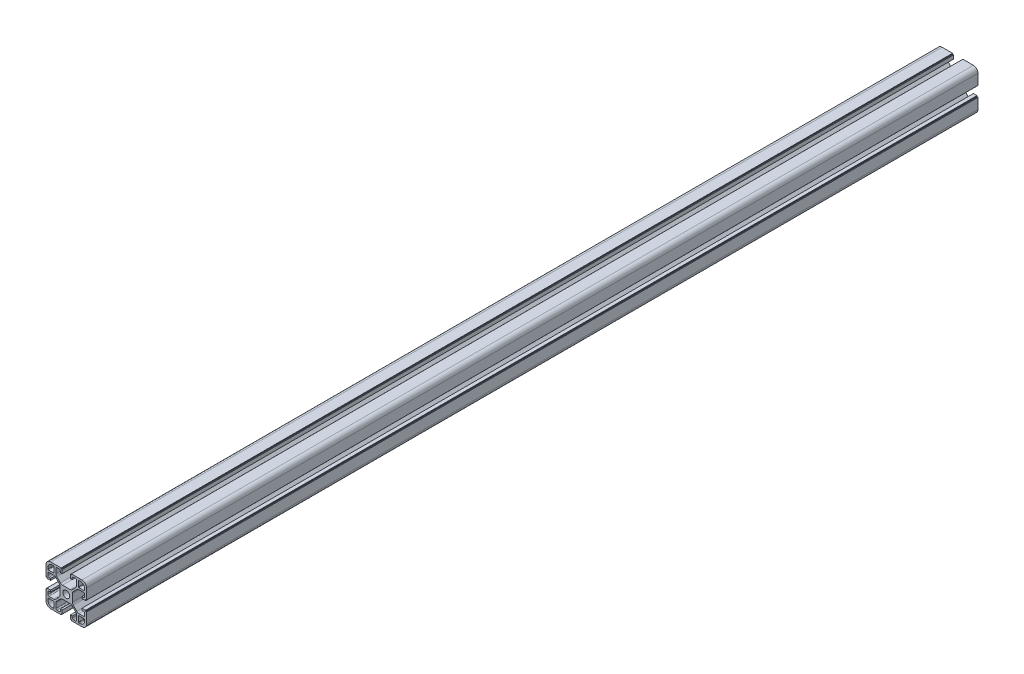
SolidWorks part; units mm, degrees
ref_plane "Front Plane" through (0, 0, 0) normal (0, 0, 1) x (1, 0, 0)
ref_plane "Top Plane" through (0, 0, 0) normal (0, 1, 0) x (1, 0, 0)
ref_plane "Right Plane" through (0, 0, 0) normal (1, 0, 0) x (0, 0, -1)
sketch "Sketch2" plane through (0, 0, 0) normal (0, 0, 1) x (1, 0, 0)
  line L0 (84.1702, 31.7204) -> (84.1702, 42.1204)
  line L1 (44.1702, 62.7204) -> (44.1702, 52.3204)
  line L2 (48.6702, 27.2204) -> (59.0702, 27.2204)
  line L3 (79.6702, 67.2204) -> (69.2702, 67.2204)
  line L4 (84.1702, 52.3204) -> (84.1702, 62.7204)
  line L5 (58.8702, 67.2204) -> (48.6702, 67.2204)
  line L6 (44.1702, 42.1204) -> (44.1702, 31.7204)
  line L7 (69.2702, 27.2204) -> (79.6702, 27.2204)
  line L8 (48.6702, 27.2204) -> (59.0702, 27.2204)
  line L9 (44.1702, 42.1204) -> (44.1702, 31.7204)
  line L10 (44.1702, 42.1204) -> (44.7702, 42.1204)
  line L11 (44.9702, 42.3204) -> (44.9702, 42.9204)
  line L12 (48.6702, 43.1204) -> (45.1702, 43.1204)
  line L13 (48.6702, 41.3204) -> (48.6702, 43.1204)
  line L14 (46.9702, 41.3204) -> (48.6702, 41.3204)
  line L15 (45.9702, 37.9704) -> (45.9702, 40.3204)
  line L16 (51.6169, 36.9704) -> (46.9702, 36.9704)
  line L17 (57.2915, 41.4024) -> (53.7382, 37.8491)
  line L18 (58.1702, 50.9171) -> (58.1702, 43.5237)
  line L19 (53.7382, 56.5917) -> (57.2915, 53.0384)
  line L20 (46.9702, 57.4704) -> (51.6169, 57.4704)
  line L21 (45.9702, 54.1204) -> (45.9702, 56.4704)
  line L22 (48.6702, 53.1204) -> (46.9702, 53.1204)
  line L23 (48.6702, 51.3204) -> (48.6702, 53.1204)
  line L24 (45.1702, 51.3204) -> (48.6702, 51.3204)
  line L25 (44.9702, 51.5204) -> (44.9702, 52.1204)
  line L26 (44.7702, 52.3204) -> (44.1702, 52.3204)
  line L27 (44.1702, 62.7204) -> (44.1702, 52.3204)
  line L28 (59.0702, 67.2204) -> (48.6702, 67.2204)
  line L29 (59.0702, 67.2204) -> (59.0702, 66.6204)
  line L30 (59.2702, 66.4204) -> (60.0702, 66.4204)
  line L31 (60.0702, 62.7204) -> (60.0702, 66.4204)
  line L32 (58.2702, 62.7204) -> (60.0702, 62.7204)
  line L33 (58.2702, 64.4204) -> (58.2702, 62.7204)
  line L34 (54.9202, 65.4204) -> (57.2702, 65.4204)
  line L35 (53.9202, 59.7737) -> (53.9202, 64.4204)
  line L36 (58.3522, 54.0991) -> (54.7989, 57.6524)
  line L37 (67.8669, 53.2204) -> (60.4735, 53.2204)
  line L38 (73.5415, 57.6524) -> (69.9882, 54.0991)
  line L39 (74.4202, 64.4204) -> (74.4202, 59.7737)
  line L40 (71.0702, 65.4204) -> (73.4202, 65.4204)
  line L41 (70.0702, 62.7204) -> (70.0702, 64.4204)
  line L42 (68.2702, 62.7204) -> (70.0702, 62.7204)
  line L43 (68.2702, 66.2204) -> (68.2702, 62.7204)
  line L44 (68.4702, 66.4204) -> (69.2702, 66.4204)
  line L45 (69.2702, 66.4204) -> (69.2702, 67.2204)
  line L46 (79.6702, 67.2204) -> (69.4702, 67.2204)
  line L47 (84.1702, 52.3204) -> (84.1702, 62.7204)
  line L48 (84.1702, 52.3204) -> (83.5702, 52.3204)
  line L49 (83.3702, 52.1204) -> (83.3702, 51.5204)
  line L50 (79.6702, 51.3204) -> (83.1702, 51.3204)
  line L51 (79.6702, 53.1204) -> (79.6702, 51.3204)
  line L52 (81.3702, 53.1204) -> (79.6702, 53.1204)
  line L53 (82.3702, 56.4704) -> (82.3702, 54.1204)
  line L54 (76.7235, 57.4704) -> (81.3702, 57.4704)
  line L55 (71.0489, 53.0384) -> (74.6022, 56.5917)
  line L56 (70.1702, 43.5237) -> (70.1702, 50.9171)
  line L57 (74.6022, 37.8491) -> (71.0489, 41.4024)
  line L58 (81.3702, 36.9704) -> (76.7235, 36.9704)
  line L59 (82.3702, 40.3204) -> (82.3702, 37.9704)
  line L60 (79.6702, 41.3204) -> (81.3702, 41.3204)
  line L61 (79.6702, 43.1204) -> (79.6702, 41.3204)
  line L62 (83.1702, 43.1204) -> (79.6702, 43.1204)
  line L63 (83.3702, 42.9204) -> (83.3702, 42.3204)
  line L64 (83.5702, 42.1204) -> (84.1702, 42.1204)
  line L65 (84.1702, 31.7204) -> (84.1702, 42.1204)
  line L66 (69.2702, 27.2204) -> (79.6702, 27.2204)
  line L67 (69.2702, 27.2204) -> (69.2702, 27.8204)
  line L68 (69.0702, 28.0204) -> (68.4702, 28.0204)
  line L69 (68.2702, 31.7204) -> (68.2702, 28.2204)
  line L70 (70.0702, 31.7204) -> (68.2702, 31.7204)
  line L71 (70.0702, 30.0204) -> (70.0702, 31.7204)
  line L72 (73.4202, 29.0204) -> (71.0702, 29.0204)
  line L73 (74.4202, 34.6671) -> (74.4202, 30.0204)
  line L74 (69.9882, 40.3417) -> (73.5415, 36.7884)
  line L75 (60.4735, 41.2204) -> (67.8669, 41.2204)
  line L76 (54.7989, 36.7884) -> (58.3522, 40.3417)
  line L77 (53.9202, 30.0204) -> (53.9202, 34.6671)
  line L78 (57.2702, 29.0204) -> (54.9202, 29.0204)
  line L79 (58.2702, 31.7204) -> (58.2702, 30.0204)
  line L80 (60.0702, 31.7204) -> (58.2702, 31.7204)
  line L81 (60.0702, 28.2204) -> (60.0702, 31.7204)
  line L82 (59.8702, 28.0204) -> (59.2702, 28.0204)
  line L83 (59.0702, 27.8204) -> (59.0702, 27.2204)
  line L84 (82.3702, 34.6704) -> (82.3702, 33.5204)
  line L85 (76.7202, 35.1704) -> (81.8702, 35.1704)
  line L86 (76.2202, 29.5204) -> (76.2202, 34.6704)
  line L87 (77.8702, 29.0204) -> (76.7202, 29.0204)
  line L88 (51.6202, 29.0204) -> (50.4702, 29.0204)
  line L89 (52.1202, 34.6704) -> (52.1202, 29.5204)
  line L90 (46.4702, 35.1704) -> (51.6202, 35.1704)
  line L91 (45.9702, 33.5204) -> (45.9702, 34.6704)
  line L92 (45.9702, 59.7704) -> (45.9702, 60.9204)
  line L93 (51.6202, 59.2704) -> (46.4702, 59.2704)
  line L94 (52.1202, 64.9204) -> (52.1202, 59.7704)
  line L95 (50.4702, 65.4204) -> (51.6202, 65.4204)
  line L96 (76.7202, 65.4204) -> (77.8702, 65.4204)
  line L97 (76.2202, 59.7704) -> (76.2202, 64.9204)
  line L98 (81.8702, 59.2704) -> (76.7202, 59.2704)
  line L99 (82.3702, 60.9204) -> (82.3702, 59.7704)
  line L100 (71.0702, 65.4204) -> (73.4202, 65.4204)
  line L101 (70.0702, 62.7204) -> (70.0702, 64.4204)
  line L102 (68.2702, 62.7204) -> (70.0702, 62.7204)
  line L103 (68.2702, 66.2204) -> (68.2702, 62.7204)
  line L104 (60.0702, 62.7204) -> (60.0702, 66.2204)
  line L105 (58.2702, 62.7204) -> (60.0702, 62.7204)
  line L106 (58.2702, 64.4204) -> (58.2702, 62.7204)
  line L107 (54.9202, 65.4204) -> (57.2702, 65.4204)
  line L108 (53.9202, 59.7737) -> (53.9202, 64.4204)
  line L109 (58.3522, 54.0991) -> (54.7989, 57.6524)
  line L110 (67.8669, 53.2204) -> (60.4735, 53.2204)
  line L111 (73.5415, 57.6524) -> (69.9882, 54.0991)
  line L112 (74.4202, 64.4204) -> (74.4202, 59.7737)
  line L113 (59.2702, 66.4204) -> (59.8702, 66.4204)
  line L114 (59.0702, 67.0204) -> (59.0702, 66.6204)
  line L115 (69.2702, 66.6204) -> (69.2702, 67.0204)
  line L116 (68.4702, 66.4204) -> (69.0702, 66.4204)
  line L117 (82.3702, 40.3204) -> (82.3702, 37.9704)
  line L118 (79.6702, 41.3204) -> (81.3702, 41.3204)
  line L119 (79.6702, 43.1204) -> (79.6702, 41.3204)
  line L120 (83.1702, 43.1204) -> (79.6702, 43.1204)
  line L121 (79.6702, 51.3204) -> (83.1702, 51.3204)
  line L122 (79.6702, 53.1204) -> (79.6702, 51.3204)
  line L123 (81.3702, 53.1204) -> (79.6702, 53.1204)
  line L124 (82.3702, 56.4704) -> (82.3702, 54.1204)
  line L125 (76.7235, 57.4704) -> (81.3702, 57.4704)
  line L126 (71.0489, 53.0384) -> (74.6022, 56.5917)
  line L127 (70.1702, 43.5237) -> (70.1702, 50.9171)
  line L128 (74.6022, 37.8491) -> (71.0489, 41.4024)
  line L129 (81.3702, 36.9704) -> (76.7235, 36.9704)
  line L130 (45.9702, 54.1204) -> (45.9702, 56.4704)
  line L131 (48.6702, 53.1204) -> (46.9702, 53.1204)
  line L132 (48.6702, 51.3204) -> (48.6702, 53.1204)
  line L133 (45.1702, 51.3204) -> (48.6702, 51.3204)
  line L134 (48.6702, 43.1204) -> (45.1702, 43.1204)
  line L135 (48.6702, 41.3204) -> (48.6702, 43.1204)
  line L136 (46.9702, 41.3204) -> (48.6702, 41.3204)
  line L137 (45.9702, 37.9704) -> (45.9702, 40.3204)
  line L138 (51.6169, 36.9704) -> (46.9702, 36.9704)
  line L139 (57.2915, 41.4024) -> (53.7382, 37.8491)
  line L140 (58.1702, 50.9171) -> (58.1702, 43.5237)
  line L141 (53.7382, 56.5917) -> (57.2915, 53.0384)
  line L142 (46.9702, 57.4704) -> (51.6169, 57.4704)
  line L143 (57.2702, 29.0204) -> (54.9202, 29.0204)
  line L144 (58.2702, 31.7204) -> (58.2702, 30.0204)
  line L145 (60.0702, 31.7204) -> (58.2702, 31.7204)
  line L146 (60.0702, 28.2204) -> (60.0702, 31.7204)
  line L147 (68.2702, 31.7204) -> (68.2702, 28.2204)
  line L148 (70.0702, 31.7204) -> (68.2702, 31.7204)
  line L149 (70.0702, 30.0204) -> (70.0702, 31.7204)
  line L150 (73.4202, 29.0204) -> (71.0702, 29.0204)
  line L151 (74.4202, 34.6671) -> (74.4202, 30.0204)
  line L152 (69.9882, 40.3417) -> (73.5415, 36.7884)
  line L153 (60.4735, 41.2204) -> (67.8669, 41.2204)
  line L154 (54.7989, 36.7884) -> (58.3522, 40.3417)
  line L155 (53.9202, 30.0204) -> (53.9202, 34.6671)
  line L156 (69.0702, 28.0204) -> (68.4702, 28.0204)
  line L157 (69.2702, 27.2204) -> (69.2702, 27.8204)
  line L158 (59.0702, 27.8204) -> (59.0702, 27.2204)
  line L159 (59.8702, 28.0204) -> (59.2702, 28.0204)
  line L160 (44.9702, 42.3204) -> (44.9702, 42.9204)
  line L161 (44.1702, 42.1204) -> (44.7702, 42.1204)
  line L162 (44.7702, 52.3204) -> (44.1702, 52.3204)
  line L163 (44.9702, 51.5204) -> (44.9702, 52.1204)
  line L164 (83.3702, 52.1204) -> (83.3702, 51.5204)
  line L165 (84.1702, 52.3204) -> (83.5702, 52.3204)
  line L166 (83.5702, 42.1204) -> (84.1702, 42.1204)
  line L167 (83.3702, 42.9204) -> (83.3702, 42.3204)
  line L168 (76.2202, 59.7704) -> (76.2202, 64.9204)
  line L169 (81.8702, 59.2704) -> (76.7202, 59.2704)
  line L170 (82.3702, 60.9204) -> (82.3702, 59.7704)
  line L171 (76.7202, 65.4204) -> (77.8702, 65.4204)
  line L172 (51.6202, 59.2704) -> (46.4702, 59.2704)
  line L173 (52.1202, 64.9204) -> (52.1202, 59.7704)
  line L174 (50.4702, 65.4204) -> (51.6202, 65.4204)
  line L175 (45.9702, 59.7704) -> (45.9702, 60.9204)
  line L176 (52.1202, 34.6704) -> (52.1202, 29.5204)
  line L177 (46.4702, 35.1704) -> (51.6202, 35.1704)
  line L178 (45.9702, 33.5204) -> (45.9702, 34.6704)
  line L179 (51.6202, 29.0204) -> (50.4702, 29.0204)
  line L180 (76.7202, 35.1704) -> (81.8702, 35.1704)
  line L181 (76.2202, 29.5204) -> (76.2202, 34.6704)
  line L182 (77.8702, 29.0204) -> (76.7202, 29.0204)
  line L183 (82.3702, 34.6704) -> (82.3702, 33.5204)
  arc A0 (60.7702, 47.2204) -> (67.5702, 47.2204) centre (64.1702, 47.2204) ccw
  arc A1 (44.1702, 31.7204) -> (48.6702, 27.2204) centre (48.6702, 31.7204) ccw
  arc A2 (44.7702, 42.1204) -> (44.9702, 42.3204) centre (44.7702, 42.3204) ccw
  arc A3 (45.1702, 43.1204) -> (44.9702, 42.9204) centre (45.1702, 42.9204) ccw
  arc A4 (46.9702, 41.3204) -> (45.9702, 40.3204) centre (46.9702, 40.3204) ccw
  arc A5 (45.9702, 37.9704) -> (46.9702, 36.9704) centre (46.9702, 37.9704) ccw
  arc A6 (51.6169, 36.9704) -> (53.7382, 37.8491) centre (51.6169, 39.9704) ccw
  arc A7 (57.2915, 41.4024) -> (58.1702, 43.5237) centre (55.1702, 43.5237) ccw
  arc A8 (58.1702, 50.9171) -> (57.2915, 53.0384) centre (55.1702, 50.9171) ccw
  arc A9 (53.7382, 56.5917) -> (51.6169, 57.4704) centre (51.6169, 54.4704) ccw
  arc A10 (46.9702, 57.4704) -> (45.9702, 56.4704) centre (46.9702, 56.4704) ccw
  arc A11 (45.9702, 54.1204) -> (46.9702, 53.1204) centre (46.9702, 54.1204) ccw
  arc A12 (44.9702, 51.5204) -> (45.1702, 51.3204) centre (45.1702, 51.5204) ccw
  arc A13 (44.9702, 52.1204) -> (44.7702, 52.3204) centre (44.7702, 52.1204) ccw
  arc A14 (48.6702, 67.2204) -> (44.1702, 62.7204) centre (48.6702, 62.7204) ccw
  arc A15 (59.0702, 66.6204) -> (59.2702, 66.4204) centre (59.2702, 66.6204) ccw
  arc A16 (58.2702, 64.4204) -> (57.2702, 65.4204) centre (57.2702, 64.4204) ccw
  arc A17 (54.9202, 65.4204) -> (53.9202, 64.4204) centre (54.9202, 64.4204) ccw
  arc A18 (53.9202, 59.7737) -> (54.7989, 57.6524) centre (56.9202, 59.7737) ccw
  arc A19 (58.3522, 54.0991) -> (60.4735, 53.2204) centre (60.4735, 56.2204) ccw
  arc A20 (67.8669, 53.2204) -> (69.9882, 54.0991) centre (67.8669, 56.2204) ccw
  arc A21 (73.5415, 57.6524) -> (74.4202, 59.7737) centre (71.4202, 59.7737) ccw
  arc A22 (74.4202, 64.4204) -> (73.4202, 65.4204) centre (73.4202, 64.4204) ccw
  arc A23 (71.0702, 65.4204) -> (70.0702, 64.4204) centre (71.0702, 64.4204) ccw
  arc A24 (68.4702, 66.4204) -> (68.2702, 66.2204) centre (68.4702, 66.2204) ccw
  arc A25 (84.1702, 62.7204) -> (79.6702, 67.2204) centre (79.6702, 62.7204) ccw
  arc A26 (83.5702, 52.3204) -> (83.3702, 52.1204) centre (83.5702, 52.1204) ccw
  arc A27 (83.1702, 51.3204) -> (83.3702, 51.5204) centre (83.1702, 51.5204) ccw
  arc A28 (81.3702, 53.1204) -> (82.3702, 54.1204) centre (81.3702, 54.1204) ccw
  arc A29 (82.3702, 56.4704) -> (81.3702, 57.4704) centre (81.3702, 56.4704) ccw
  arc A30 (76.7235, 57.4704) -> (74.6022, 56.5917) centre (76.7235, 54.4704) ccw
  arc A31 (71.0489, 53.0384) -> (70.1702, 50.9171) centre (73.1702, 50.9171) ccw
  arc A32 (70.1702, 43.5237) -> (71.0489, 41.4024) centre (73.1702, 43.5237) ccw
  arc A33 (74.6022, 37.8491) -> (76.7235, 36.9704) centre (76.7235, 39.9704) ccw
  arc A34 (81.3702, 36.9704) -> (82.3702, 37.9704) centre (81.3702, 37.9704) ccw
  arc A35 (82.3702, 40.3204) -> (81.3702, 41.3204) centre (81.3702, 40.3204) ccw
  arc A36 (83.3702, 42.9204) -> (83.1702, 43.1204) centre (83.1702, 42.9204) ccw
  arc A37 (83.3702, 42.3204) -> (83.5702, 42.1204) centre (83.5702, 42.3204) ccw
  arc A38 (79.6702, 27.2204) -> (84.1702, 31.7204) centre (79.6702, 31.7204) ccw
  arc A39 (69.2702, 27.8204) -> (69.0702, 28.0204) centre (69.0702, 27.8204) ccw
  arc A40 (68.2702, 28.2204) -> (68.4702, 28.0204) centre (68.4702, 28.2204) ccw
  arc A41 (70.0702, 30.0204) -> (71.0702, 29.0204) centre (71.0702, 30.0204) ccw
  arc A42 (73.4202, 29.0204) -> (74.4202, 30.0204) centre (73.4202, 30.0204) ccw
  arc A43 (74.4202, 34.6671) -> (73.5415, 36.7884) centre (71.4202, 34.6671) ccw
  arc A44 (69.9882, 40.3417) -> (67.8669, 41.2204) centre (67.8669, 38.2204) ccw
  arc A45 (60.4735, 41.2204) -> (58.3522, 40.3417) centre (60.4735, 38.2204) ccw
  arc A46 (54.7989, 36.7884) -> (53.9202, 34.6671) centre (56.9202, 34.6671) ccw
  arc A47 (53.9202, 30.0204) -> (54.9202, 29.0204) centre (54.9202, 30.0204) ccw
  arc A48 (57.2702, 29.0204) -> (58.2702, 30.0204) centre (57.2702, 30.0204) ccw
  arc A49 (59.8702, 28.0204) -> (60.0702, 28.2204) centre (59.8702, 28.2204) ccw
  arc A50 (59.2702, 28.0204) -> (59.0702, 27.8204) centre (59.2702, 27.8204) ccw
  arc A51 (82.3702, 34.6704) -> (81.8702, 35.1704) centre (81.8702, 34.6704) ccw
  arc A52 (76.7202, 35.1704) -> (76.2202, 34.6704) centre (76.7202, 34.6704) ccw
  arc A53 (76.2202, 29.5204) -> (76.7202, 29.0204) centre (76.7202, 29.5204) ccw
  arc A54 (77.8702, 29.0204) -> (82.3702, 33.5204) centre (77.8702, 33.5204) ccw
  arc A55 (51.6202, 29.0204) -> (52.1202, 29.5204) centre (51.6202, 29.5204) ccw
  arc A56 (52.1202, 34.6704) -> (51.6202, 35.1704) centre (51.6202, 34.6704) ccw
  arc A57 (46.4702, 35.1704) -> (45.9702, 34.6704) centre (46.4702, 34.6704) ccw
  arc A58 (45.9702, 33.5204) -> (50.4702, 29.0204) centre (50.4702, 33.5204) ccw
  arc A59 (45.9702, 59.7704) -> (46.4702, 59.2704) centre (46.4702, 59.7704) ccw
  arc A60 (51.6202, 59.2704) -> (52.1202, 59.7704) centre (51.6202, 59.7704) ccw
  arc A61 (52.1202, 64.9204) -> (51.6202, 65.4204) centre (51.6202, 64.9204) ccw
  arc A62 (50.4702, 65.4204) -> (45.9702, 60.9204) centre (50.4702, 60.9204) ccw
  arc A63 (76.7202, 65.4204) -> (76.2202, 64.9204) centre (76.7202, 64.9204) ccw
  arc A64 (76.2202, 59.7704) -> (76.7202, 59.2704) centre (76.7202, 59.7704) ccw
  arc A65 (81.8702, 59.2704) -> (82.3702, 59.7704) centre (81.8702, 59.7704) ccw
  arc A66 (82.3702, 60.9204) -> (77.8702, 65.4204) centre (77.8702, 60.9204) ccw
  arc A67 (67.5702, 47.2204) -> (60.7702, 47.2204) centre (64.1702, 47.2204) ccw
  arc A68 (60.7702, 47.2204) -> (67.5702, 47.2204) centre (64.1702, 47.2204) ccw
  arc A69 (67.5702, 47.2204) -> (60.7702, 47.2204) centre (64.1702, 47.2204) ccw
  arc A70 (71.0702, 65.4204) -> (70.0702, 64.4204) centre (71.0702, 64.4204) ccw
  arc A71 (54.9202, 65.4204) -> (53.9202, 64.4204) centre (54.9202, 64.4204) ccw
  arc A72 (58.2702, 64.4204) -> (57.2702, 65.4204) centre (57.2702, 64.4204) ccw
  arc A73 (74.4202, 64.4204) -> (73.4202, 65.4204) centre (73.4202, 64.4204) ccw
  arc A74 (68.4702, 66.4204) -> (68.2702, 66.2204) centre (68.4702, 66.2204) ccw
  arc A75 (59.0702, 66.6204) -> (59.2702, 66.4204) centre (59.2702, 66.6204) ccw
  arc A76 (82.3702, 40.3204) -> (81.3702, 41.3204) centre (81.3702, 40.3204) ccw
  arc A77 (82.3702, 56.4704) -> (81.3702, 57.4704) centre (81.3702, 56.4704) ccw
  arc A78 (81.3702, 53.1204) -> (82.3702, 54.1204) centre (81.3702, 54.1204) ccw
  arc A79 (81.3702, 36.9704) -> (82.3702, 37.9704) centre (81.3702, 37.9704) ccw
  arc A80 (57.2702, 29.0204) -> (58.2702, 30.0204) centre (57.2702, 30.0204) ccw
  arc A81 (73.4202, 29.0204) -> (74.4202, 30.0204) centre (73.4202, 30.0204) ccw
  arc A82 (70.0702, 30.0204) -> (71.0702, 29.0204) centre (71.0702, 30.0204) ccw
  arc A83 (53.9202, 30.0204) -> (54.9202, 29.0204) centre (54.9202, 30.0204) ccw
  arc A84 (45.9702, 54.1204) -> (46.9702, 53.1204) centre (46.9702, 54.1204) ccw
  arc A85 (45.9702, 37.9704) -> (46.9702, 36.9704) centre (46.9702, 37.9704) ccw
  arc A86 (46.9702, 41.3204) -> (45.9702, 40.3204) centre (46.9702, 40.3204) ccw
  arc A87 (46.9702, 57.4704) -> (45.9702, 56.4704) centre (46.9702, 56.4704) ccw
  arc A88 (83.1702, 51.3204) -> (83.3702, 51.5204) centre (83.1702, 51.5204) ccw
  arc A89 (83.3702, 42.9204) -> (83.1702, 43.1204) centre (83.1702, 42.9204) ccw
  arc A90 (83.3702, 42.3204) -> (83.5702, 42.1204) centre (83.5702, 42.3204) ccw
  arc A91 (83.5702, 52.3204) -> (83.3702, 52.1204) centre (83.5702, 52.1204) ccw
  arc A92 (68.2702, 28.2204) -> (68.4702, 28.0204) centre (68.4702, 28.2204) ccw
  arc A93 (59.8702, 28.0204) -> (60.0702, 28.2204) centre (59.8702, 28.2204) ccw
  arc A94 (59.2702, 28.0204) -> (59.0702, 27.8204) centre (59.2702, 27.8204) ccw
  arc A95 (69.2702, 27.8204) -> (69.0702, 28.0204) centre (69.0702, 27.8204) ccw
  arc A96 (45.1702, 43.1204) -> (44.9702, 42.9204) centre (45.1702, 42.9204) ccw
  arc A97 (44.9702, 51.5204) -> (45.1702, 51.3204) centre (45.1702, 51.5204) ccw
  arc A98 (44.9702, 52.1204) -> (44.7702, 52.3204) centre (44.7702, 52.1204) ccw
  arc A99 (44.7702, 42.1204) -> (44.9702, 42.3204) centre (44.7702, 42.3204) ccw
  arc A100 (44.1702, 31.7204) -> (48.6702, 27.2204) centre (48.6702, 31.7204) ccw
  arc A101 (79.6702, 27.2204) -> (84.1702, 31.7204) centre (79.6702, 31.7204) ccw
  arc A102 (48.6702, 67.2204) -> (44.1702, 62.7204) centre (48.6702, 62.7204) ccw
  arc A103 (84.1702, 62.7204) -> (79.6702, 67.2204) centre (79.6702, 62.7204) ccw
  arc A104 (82.3702, 60.9204) -> (77.8702, 65.4204) centre (77.8702, 60.9204) ccw
  arc A105 (81.8702, 59.2704) -> (82.3702, 59.7704) centre (81.8702, 59.7704) ccw
  arc A106 (76.7202, 65.4204) -> (76.2202, 64.9204) centre (76.7202, 64.9204) ccw
  arc A107 (76.2202, 59.7704) -> (76.7202, 59.2704) centre (76.7202, 59.7704) ccw
  arc A108 (50.4702, 65.4204) -> (45.9702, 60.9204) centre (50.4702, 60.9204) ccw
  arc A109 (45.9702, 33.5204) -> (50.4702, 29.0204) centre (50.4702, 33.5204) ccw
  arc A110 (77.8702, 29.0204) -> (82.3702, 33.5204) centre (77.8702, 33.5204) ccw
  arc A111 (76.2202, 29.5204) -> (76.7202, 29.0204) centre (76.7202, 29.5204) ccw
  arc A112 (82.3702, 34.6704) -> (81.8702, 35.1704) centre (81.8702, 34.6704) ccw
  arc A113 (76.7202, 35.1704) -> (76.2202, 34.6704) centre (76.7202, 34.6704) ccw
  arc A114 (46.4702, 35.1704) -> (45.9702, 34.6704) centre (46.4702, 34.6704) ccw
  arc A115 (51.6202, 29.0204) -> (52.1202, 29.5204) centre (51.6202, 29.5204) ccw
  arc A116 (52.1202, 34.6704) -> (51.6202, 35.1704) centre (51.6202, 34.6704) ccw
  arc A117 (52.1202, 64.9204) -> (51.6202, 65.4204) centre (51.6202, 64.9204) ccw
  arc A118 (45.9702, 59.7704) -> (46.4702, 59.2704) centre (46.4702, 59.7704) ccw
  arc A119 (51.6202, 59.2704) -> (52.1202, 59.7704) centre (51.6202, 59.7704) ccw
  arc A120 (74.6022, 37.8491) -> (76.7235, 36.9704) centre (76.7235, 39.9704) ccw
  arc A121 (70.1702, 43.5237) -> (71.0489, 41.4024) centre (73.1702, 43.5237) ccw
  arc A122 (74.4202, 34.6671) -> (73.5415, 36.7884) centre (71.4202, 34.6671) ccw
  arc A123 (69.9882, 40.3417) -> (67.8669, 41.2204) centre (67.8669, 38.2204) ccw
  arc A124 (54.7989, 36.7884) -> (53.9202, 34.6671) centre (56.9202, 34.6671) ccw
  arc A125 (60.4735, 41.2204) -> (58.3522, 40.3417) centre (60.4735, 38.2204) ccw
  arc A126 (51.6169, 36.9704) -> (53.7382, 37.8491) centre (51.6169, 39.9704) ccw
  arc A127 (57.2915, 41.4024) -> (58.1702, 43.5237) centre (55.1702, 43.5237) ccw
  arc A128 (58.1702, 50.9171) -> (57.2915, 53.0384) centre (55.1702, 50.9171) ccw
  arc A129 (53.7382, 56.5917) -> (51.6169, 57.4704) centre (51.6169, 54.4704) ccw
  arc A130 (53.9202, 59.7737) -> (54.7989, 57.6524) centre (56.9202, 59.7737) ccw
  arc A131 (58.3522, 54.0991) -> (60.4735, 53.2204) centre (60.4735, 56.2204) ccw
  arc A132 (67.8669, 53.2204) -> (69.9882, 54.0991) centre (67.8669, 56.2204) ccw
  arc A133 (71.0489, 53.0384) -> (70.1702, 50.9171) centre (73.1702, 50.9171) ccw
  arc A134 (76.7235, 57.4704) -> (74.6022, 56.5917) centre (76.7235, 54.4704) ccw
  arc A135 (73.5415, 57.6524) -> (74.4202, 59.7737) centre (71.4202, 59.7737) ccw
extrude "Boss-Extrude1" add sketch "Sketch2" along normal blind 880 contours A50 L82 A49 L81 L80 L79 A48 L78 A47 L77 A46 L76 A45 L75 A44 L74 A43 L73 A42 L72 A41 L71 L70 L69 A40 L68 A39 L67 L7 A38 L0 L64 A37 L63 A36 L62 L61 L60 A35 L59 A34 L58 A33 L57 A32 L56 A31 L55 A30 L54 A29
